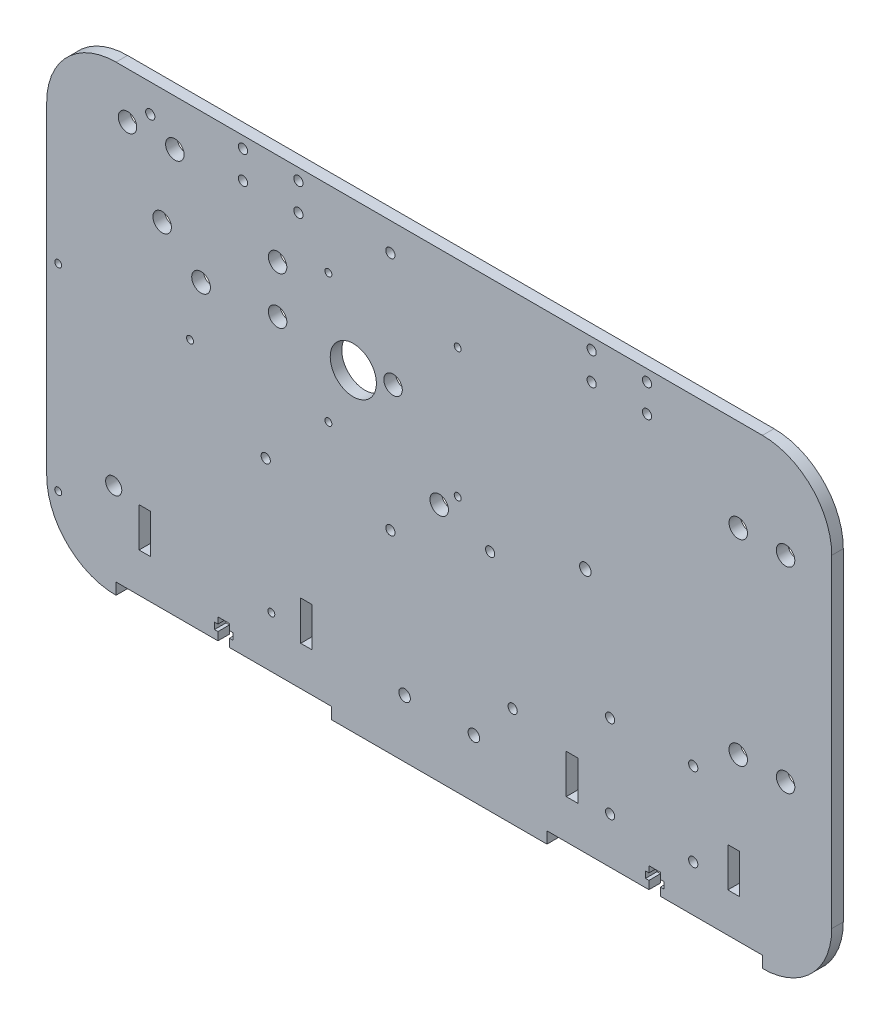
SolidWorks part; units mm, degrees
ref_plane "Alzado" through (0, 0, 0) normal (0, 0, 1) x (1, 0, 0)
ref_plane "Planta" through (0, 0, 0) normal (0, 1, 0) x (1, 0, 0)
ref_plane "Vista lateral" through (0, 0, 0) normal (1, 0, 0) x (0, 0, -1)
sketch "Croquis1" plane through (0, 0, 0) normal (0, 0, 1) x (1, 0, 0)
  line L1 (30, 0) -> (310, 0)
  line L2 (0, 30) -> (0, 170)
  line L3 (30, 200) -> (310, 200)
  line L4 (340, 30) -> (340, 170)
  arc A0 (30, 0) -> (0, 30) centre (30, 30) cw
  arc A1 (310, 0) -> (340, 30) centre (310, 30) ccw
  arc A2 (310, 200) -> (340, 170) centre (310, 170) cw
  arc A3 (0, 170) -> (30, 200) centre (30, 170) cw
  point P7 (0, 0)
  point P12 (340, 200)
  point P15 (0, 200)
  dimension "D3" = 30
  dimension "D1" = 200
  dimension "D2" = 340
extrude "Saliente-Extruir1" add sketch "Croquis1" along normal blind 5
sketch "Croquis2" plane through (0, 0, 5) normal (0, 0, -1) x (-1, 0, 0)
  line L0 (-55.5, 180) -> (-35, 180) construction
  line L2 (-310, 200) -> (-30, 200) construction
  line L3 (0, 170) -> (0, 30) construction
  line L4 (-100, 160) -> (-100, 139.5) construction
  line L5 (-310, 200) -> (-30, 200) construction
  line L6 (-299.5, 160) -> (-320, 160) construction
  line L7 (-340, 30) -> (-340, 170) construction
  line L8 (-320, 75) -> (-299.5, 75) construction
  line L9 (-30, 0) -> (-310, 0) construction
  line L10 (-100, 149.75) -> (-146.5265, 149.75) construction
  circle A0 centre (-55.5, 180) radius 4
  circle A1 centre (-35, 180) radius 4
  circle A2 centre (-100, 160) radius 4
  circle A3 centre (-100, 139.5) radius 4
  circle A4 centre (-299.5, 160) radius 4
  circle A5 centre (-320, 160) radius 4
  circle A6 centre (-320, 75) radius 4
  circle A7 centre (-299.5, 75) radius 4
  circle A8 centre (-150, 139) radius 4
  circle A9 centre (-170, 104) radius 4
  circle A10 centre (-50, 150) radius 4
  dimension "D1" = 8
  dimension "D10" = 40
  dimension "D14" = 8
  dimension "D19" = 8
  dimension "D2" = 20.5
  dimension "D3" = 35
  dimension "D4" = 20
  dimension "D5" = 20.5
  dimension "D6" = 40
  dimension "D7" = 100
  dimension "D8" = 20.5
  dimension "D9" = 20
  dimension "D11" = 20.5
  dimension "D12" = 20
  dimension "D13" = 75
  dimension "D15" = 150
  dimension "D16" = 61
  dimension "D17" = 35
  dimension "D18" = 20
  dimension "D20" = 50
  dimension "D21" = 50
extrude "Cortar-Extruir4" cut sketch "Croquis2" along normal blind 10
sketch "Croquis3" plane through (0, 0, 0) normal (0, 0, -1) x (-1, 0, 0)
  line L0 (-44.85, 187.84) -> (-148.85, 187.84) construction
  line L1 (-148.85, 187.84) -> (-148.85, 83.84) construction
  line L2 (-148.85, 83.84) -> (-94.85, 83.84) construction
  line L3 (-94.85, 83.84) -> (-44.85, 187.84) construction
  line L4 (-310, 200) -> (-30, 200) construction
  line L5 (0, 170) -> (0, 30) construction
  circle A0 centre (-148.85, 83.84) radius 2
  circle A1 centre (-94.85, 83.84) radius 2
  circle A2 centre (-44.85, 187.84) radius 2
  circle A3 centre (-148.85, 187.84) radius 2
  circle A4 centre (-132.79, 135.84) radius 10
  circle A5 centre (-66.85, 135.84) radius 4.05
  dimension "D1" = 4
  dimension "D5" = 20
  dimension "D6" = 8.1
  dimension "D2" = 104
  dimension "D3" = 104
  dimension "D4" = 54
  dimension "D7" = 16.06
  dimension "D8" = 52
  dimension "D9" = 52
  dimension "D10" = 82
  dimension "D11" = 12.16
  dimension "D12" = 66.85
extrude "Cortar-Extruir5" cut sketch "Croquis3" against normal blind 10
sketch "Croquis5" plane through (0, 0, 0) normal (0, 0, -1) x (-1, 0, 0)
  line L0 (-178, 167) -> (-122, 167) construction
  line L1 (-122, 167) -> (-122, 111) construction
  line L2 (-178, 167) -> (-178, 111) construction
  line L3 (-178, 111) -> (-122, 111) construction
  line L4 (-310, 200) -> (-30, 200) construction
  line L7 (0, 170) -> (0, 30) construction
  circle A0 centre (-178, 167) radius 1.5
  circle A1 centre (-122, 111) radius 1.5
  circle A2 centre (-122, 167) radius 1.5
  circle A3 centre (-178, 111) radius 1.5
  dimension "D1" = 3
  dimension "D4" = 3
  dimension "D2" = 56
  dimension "D3" = 56
  dimension "D5" = 33
  dimension "D6" = 122
extrude "Cortar-Extruir6" cut sketch "Croquis5" against normal blind 10
sketch "Croquis6" plane through (0, 0, 5) normal (0, 0, 1) x (1, 0, 0)
  line L0 (244, 61) -> (280, 61) construction
  line L1 (244, 61) -> (244, 25) construction
  line L2 (244, 25) -> (280, 25) construction
  line L3 (280, 25) -> (280, 61) construction
  line L4 (340, 30) -> (340, 170) construction
  line L5 (30, 0) -> (310, 0) construction
  circle A0 centre (244, 61) radius 2
  circle A1 centre (280, 61) radius 2
  circle A2 centre (244, 25) radius 2
  circle A3 centre (280, 25) radius 2
  dimension "D1" = 4
  dimension "D2" = 36
  dimension "D3" = 36
  dimension "D4" = 60
  dimension "D5" = 25
extrude "Cortar-Extruir7" cut sketch "Croquis6" against normal blind 10
sketch "Croquis7" plane through (0, 0, 5) normal (0, 0, 1) x (1, 0, 0)
  line L4 (30, 0) -> (310, 0)
  line L5 (340, 30) -> (340, 170)
  line L6 (310, 200) -> (30, 200)
  line L7 (0, 170) -> (0, 30)
  line L8 (30, 0) -> (310, 0)
  line L9 (340, 30) -> (340, 170)
  line L10 (310, 200) -> (30, 200)
  line L11 (0, 170) -> (0, 30)
  circle A0 centre (50, 150) radius 4 construction
  circle A1 centre (100, 160) radius 4 construction
  circle A2 centre (100, 139.5) radius 4 construction
  circle A3 centre (299.5, 75) radius 4 construction
  arc A4 (0, 30) -> (30, 0) centre (30, 30) ccw
  arc A5 (310, 0) -> (340, 30) centre (310, 30) ccw
  arc A6 (340, 170) -> (310, 200) centre (310, 170) ccw
  arc A7 (30, 200) -> (0, 170) centre (30, 170) ccw
  arc A8 (0, 30) -> (30, 0) centre (30, 30) ccw
  arc A9 (310, 0) -> (340, 30) centre (310, 30) ccw
  arc A10 (340, 170) -> (310, 200) centre (310, 170) ccw
  arc A11 (30, 200) -> (0, 170) centre (30, 170) ccw
  circle A12 centre (320, 75) radius 4 construction
  circle A13 centre (299.5, 160) radius 4 construction
  circle A14 centre (320, 160) radius 4 construction
  circle A15 centre (55.5, 180) radius 4 construction
  circle A16 centre (35, 180) radius 4 construction
  circle A17 centre (50, 150) radius 4
  circle A18 centre (100, 160) radius 4
  circle A19 centre (100, 139.5) radius 4
  circle A20 centre (299.5, 75) radius 4
  circle A21 centre (320, 75) radius 4
  circle A22 centre (299.5, 160) radius 4
  circle A23 centre (320, 160) radius 4
  circle A24 centre (55.5, 180) radius 4
  circle A25 centre (35, 180) radius 4
  dimension "D1" = 0
sketch "Croquis8" plane through (0, 0, 5) normal (0, 0, 1) x (1, 0, 0)
  line L0 (236, 195) -> (236, 183) construction
  line L1 (236, 195) -> (260, 195) construction
  line L2 (236, 183) -> (260, 183) construction
  line L3 (260, 183) -> (260, 195) construction
  line L4 (85, 195) -> (85, 183) construction
  line L5 (85, 195) -> (109, 195) construction
  line L6 (85, 183) -> (109, 183) construction
  line L7 (109, 183) -> (109, 195) construction
  line L8 (310, 200) -> (30, 200) construction
  line L9 (340, 30) -> (340, 170) construction
  line L10 (0, 170) -> (0, 30) construction
  circle A0 centre (236, 195) radius 2
  circle A1 centre (236, 183) radius 2
  circle A2 centre (260, 183) radius 2
  circle A3 centre (260, 195) radius 2
  circle A4 centre (85, 195) radius 2
  circle A5 centre (85, 183) radius 2
  circle A6 centre (109, 183) radius 2
  circle A7 centre (109, 195) radius 2
  dimension "D1" = 24
  dimension "D2" = 12
  dimension "D3" = 24
  dimension "D4" = 12
  dimension "D5" = 5
  dimension "D6" = 80
  dimension "D7" = 85
extrude "Cortar-Extruir8" cut sketch "Croquis8" against normal blind 10
sketch "Croquis9" plane through (0, 0, 0) normal (0, 0, -1) x (-1, 0, 0)
  line L0 (-233.2967, 111.4949) -> (-201.8, 43.4) construction
  line L1 (-201.8, 43.4) -> (-192.05, 97.4132) construction
  line L2 (-192.05, 97.4132) -> (-233.2967, 111.4949) construction
  line L3 (-62.0804, 111.91) -> (-4.98, 111.91) construction
  line L4 (-4.98, 111.91) -> (-4.98, 26.56) construction
  line L5 (-4.98, 26.56) -> (-97.2809, 27.16) construction
  line L6 (-62.0804, 111.91) -> (-97.2809, 27.16) construction
  line L8 (-30, 0) -> (-310, 0) construction
  line L9 (0, 170) -> (0, 30) construction
  line L10 (-340, 30) -> (-340, 170) construction
  circle A0 centre (-29.01, 40.6565) radius 3.5
  circle A1 centre (-62.0804, 111.91) radius 1.5
  circle A2 centre (-4.98, 111.91) radius 1.5
  circle A3 centre (-97.2809, 27.16) radius 1.5
  circle A4 centre (-4.98, 26.56) radius 1.5
  circle A5 centre (-233.2967, 111.4949) radius 2.5
  circle A6 centre (-201.8, 43.4) radius 2
  circle A7 centre (-192.05, 97.4132) radius 2
  dimension "D1" = 24.03
  dimension "D2" = 13.94
  dimension "D3" = 26.56
  dimension "D4" = 4.98
  dimension "D5" = 54.8862
  dimension "D6" = 43.5843
  dimension "D7" = 75.0264
  dimension "D8" = 43.4
  dimension "D9" = 138.2
extrude "Cortar-Extruir9" cut sketch "Croquis9" against normal blind 10
sketch "Croquis10" plane through (0, 0, 5) normal (0, 0, 1) x (1, 0, 0)
  line L0 (123.3333, 5) -> (123.3333, 0)
  line L1 (30, 0) -> (310, 0)
  line L2 (30, 0) -> (30, 5)
  line L3 (30, 5) -> (310, 5)
  line L4 (310, 0) -> (310, 5)
  line L5 (216.6667, 5) -> (216.6667, 0)
  point P10 (30, 2.5)
  line M48 (30, 0) -> (310, 0)
  dimension "D1" = 93.3333
  dimension "D2" = 93.3333
  dimension "D3" = 5
extrude "Cortar-Extruir10" cut sketch "Croquis10" against normal blind 10 contours L3 L2 L0 M48 | L3 L5 L1 L4
sketch "Croquis12" plane through (0, 0, 5) normal (0, 0, 1) x (1, 0, 0)
  line L0 (76.6667, 5) -> (76.6667, 14) construction
  line L1 (30, 5) -> (123.3333, 5) construction
  line L2 (170, 0) -> (170, 18.6393) construction
  line L3 (123.3333, 0) -> (216.6667, 0) construction
  line L4 (74.1667, 5) -> (74.1667, 8.5)
  line L5 (74.1667, 8.5) -> (72.6667, 8.5)
  line L6 (72.6667, 8.5) -> (72.6667, 11.3)
  line L7 (72.6667, 11.3) -> (74.1667, 11.3)
  line L8 (74.1667, 11.3) -> (74.1667, 14)
  line L9 (74.1667, 14) -> (79.1667, 14)
  line L10 (79.1667, 8.5) -> (80.6667, 8.5)
  line L11 (79.1667, 5) -> (79.1667, 8.5)
  line L12 (80.6667, 8.5) -> (80.6667, 11.3)
  line L13 (80.6667, 11.3) -> (79.1667, 11.3)
  line L14 (79.1667, 11.3) -> (79.1667, 14)
  line L15 (263.3333, 5) -> (263.3333, 14) construction
  line L16 (260.8333, 11.3) -> (260.8333, 14)
  line L17 (259.3333, 11.3) -> (260.8333, 11.3)
  line L18 (259.3333, 8.5) -> (259.3333, 11.3)
  line L19 (260.8333, 5) -> (260.8333, 8.5)
  line L20 (260.8333, 8.5) -> (259.3333, 8.5)
  line L21 (265.8333, 14) -> (260.8333, 14)
  line L22 (265.8333, 11.3) -> (265.8333, 14)
  line L23 (267.3333, 11.3) -> (265.8333, 11.3)
  line L24 (267.3333, 8.5) -> (267.3333, 11.3)
  line L25 (265.8333, 8.5) -> (267.3333, 8.5)
  line L26 (265.8333, 5) -> (265.8333, 8.5)
  line L27 (74.1667, 5) -> (79.1667, 5)
  line L28 (260.8333, 5) -> (265.8333, 5)
  point P1 (76.6667, 14)
  dimension "D1" = 2.8
  dimension "D2" = 4
  dimension "D3" = 9
  dimension "D4" = 3.5
  dimension "D5" = 2.5
extrude "Cortar-Extruir14" cut sketch "Croquis12" against normal blind 5
sketch "Croquis13" plane through (0, 0, 5) normal (0, 0, 1) x (1, 0, 0)
  line L0 (170, 0) -> (170, 28.0268) construction
  line L1 (123.3333, 0) -> (216.6667, 0) construction
  line L2 (79.1667, 5) -> (123.3333, 5) construction
  line L3 (110, 5) -> (115, 5)
  line L4 (110, 5) -> (110, 39)
  line L5 (110, 39) -> (115, 39)
  line L6 (115, 5) -> (115, 39)
  line L7 (225, 5) -> (225, 39)
  line L8 (230, 39) -> (225, 39)
  line L9 (230, 5) -> (230, 39)
  line L10 (230, 5) -> (225, 5)
  line L11 (110, 22) -> (115, 22)
  line L12 (225, 22) -> (230, 22)
  line L13 (30, 5) -> (74.1667, 5) construction
  line L14 (40, 5) -> (45, 5)
  line L15 (40, 5) -> (40, 39)
  line L16 (40, 39) -> (45, 39)
  line L17 (45, 5) -> (45, 39)
  line L18 (40, 22) -> (45, 22)
  line L19 (300, 22) -> (295, 22)
  line L20 (295, 5) -> (295, 39)
  line L21 (300, 39) -> (295, 39)
  line L22 (300, 5) -> (300, 39)
  line L23 (300, 5) -> (295, 5)
  dimension "D1" = 5
  dimension "D2" = 60
  dimension "D3" = 34
  dimension "D4" = 5
  dimension "D5" = 70
extrude "Cortar-Extruir15" cut sketch "Croquis13" against normal blind 5 contours L15 L18 L17 L16 | L4 L11 L6 L5 | L7 L12 L9 L8 | L19 L22 L21 L20
sketch "Croquis14" plane through (0, 0, 5) normal (0, 0, 1) x (1, 0, 0)
  line L0 (170, 0) -> (170, 25) construction
  line L1 (123.3333, 0) -> (216.6667, 0) construction
  line L2 (155, 25) -> (170, 25) construction
  line L3 (79.1667, 5) -> (123.3333, 5) construction
  circle A0 centre (155, 25) radius 2.5
  circle A1 centre (185, 25) radius 2.5
  dimension "D2" = 5
  dimension "D1" = 15
  dimension "D3" = 20
extrude "Cortar-Extruir16" cut sketch "Croquis14" against normal blind 10
